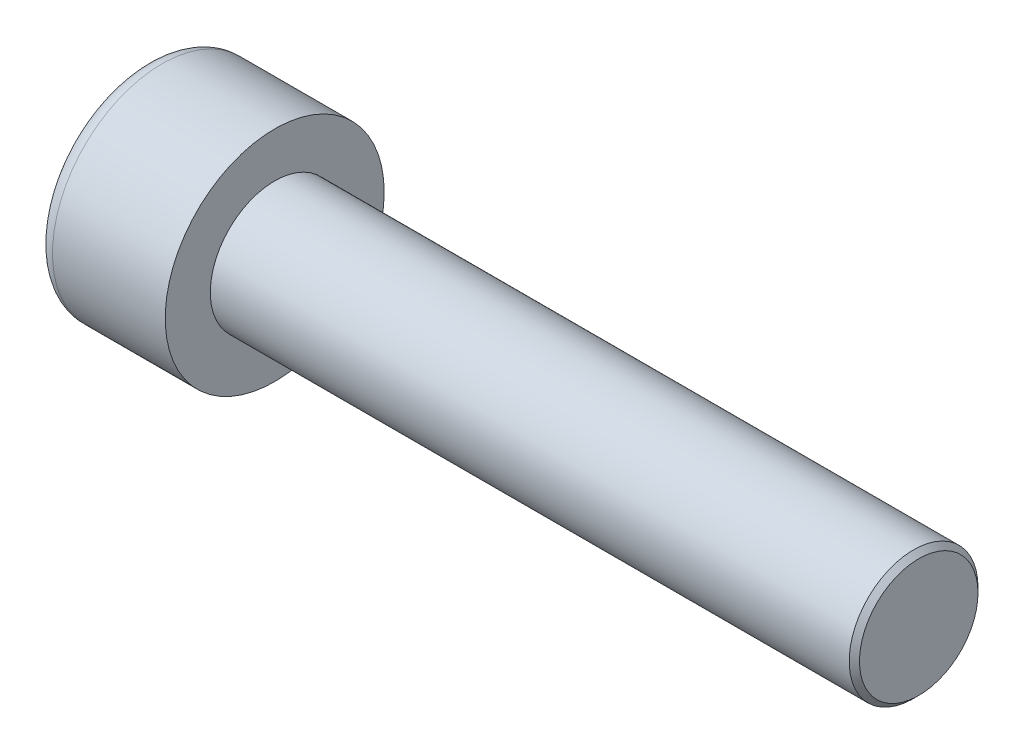
SolidWorks part; units mm, degrees
ref_plane "Front" through (0, 0, 0) normal (0, 0, 1) x (1, 0, 0)
ref_plane "Top" through (0, 0, 0) normal (0, 1, 0) x (1, 0, 0)
ref_plane "Right" through (0, 0, 0) normal (1, 0, 0) x (0, 0, -1)
sketch "Sketch1" plane through (0, 0, 0) normal (1, 0, 0) x (0, 0, -1)
  circle A0 centre (0, 0) radius 4.25
  dimension "dk" = 8.5
extrude "BaseHead" add sketch "Sketch1" along normal blind 5
sketch "Sketch2" plane through (5, 0, 0) normal (1, 0, 0) x (0, 0, -1)
  circle A0 centre (0, 0) radius 2.5
  dimension "d" = 5
extrude "BaseBody" add sketch "Sketch2" along normal blind 25
cosmetic thread "ThreadCosmetic1" parameters "b"=25, "D2"=4.134
sketch "Sketch3" plane through (0, 0, 0) normal (1, 0, 0) x (0, 0, -1)
  line L1 (2.3094, 0) -> (1.1547, 2)
  line L2 (1.1547, 2) -> (-1.1547, 2)
  line L3 (-1.1547, 2) -> (-2.3094, 0)
  line L4 (-2.3094, 0) -> (-1.1547, -2)
  line L5 (-1.1547, -2) -> (1.1547, -2)
  line L6 (1.1547, -2) -> (2.3094, 0)
  circle A0 centre (0, 0) radius 2 construction
  dimension "s" = 4
  dimension "e" = 4.6188
extrude "HexagonSocket" cut sketch "Sketch3" along normal blind 2.5
sketch "Sketch4" plane through (-4.1961, 0.75, 0) normal (0, 0, 1) x (-1, 0, 0)
  line L0 (-6.6961, 2.75) -> (-7.8508, 0.75)
  line L2 (-7.8508, 0.75) -> (-6.6961, 0.75)
  line L3 (-6.6961, 0.75) -> (-6.6961, 2.75)
  line L4 (-5.0351, 0.75) -> (0.839, 0.75) construction
  line L5 (-34.1961, 0.75) -> (-9.1961, 0.75) construction
  line L6 (-9.1961, 0.75) -> (-4.1961, 0.75) construction
  dimension "m" = 60
revolve "Cut-Revolve1" cut sketch "Sketch4" angle 360 about L4
fillet "HeadFillet" [suppressed] radius 0.2
fillet "TopFillet" radius 0.625 1 edges at (0, 0, -4.25)
chamfer "Chamfer1" distance 0.2 angle 45 1 edges at (30, 0, -2.5)
sketch "Sketch5" plane through (0, 0, 0) normal (0, 0, 1) x (1, 0, 0)
  line L0 (29.8, 2.125) -> (30.0165, 2.5)
  line L1 (30.0165, 2.5) -> (30.0165, 2.933)
  line L2 (30.0165, 2.933) -> (29.5835, 2.933)
  line L3 (29.5835, 2.933) -> (29.5835, 2.5)
  line L4 (29.5835, 2.5) -> (29.8, 2.125)
  line L5 (0, 0) -> (7.8886, 0) construction
  line L6 (29.8, -2.5) -> (29.8, 2.5) construction
  dimension "D1" = 5
  dimension "D2" = 0.433
revolve "Cut-Revolve10" [suppressed] cut sketch "Sketch5" angle 360 about L5
pattern_linear "LPattern10" [suppressed] count 48 spacing 0.5196 along (1, 0, 0)
equation "\"r1@TopFillet\" = \"d@Sketch2\" / 8"
equation "\"D1@Chamfer1\" = \"r@HeadFillet\""
equation "\"D1@Sketch5\" = \"d@Sketch2\""
equation "\"D2@Sketch5\" =  ( \"d@Sketch2\" - \"D2@ThreadCosmetic1\" )  / 2"
equation "\"D3@LPattern10\" = \"D2@Sketch5\" * 1.2"
equation "\"D1@LPattern10\" = \"b@ThreadCosmetic1\" / \"D3@LPattern10\""
